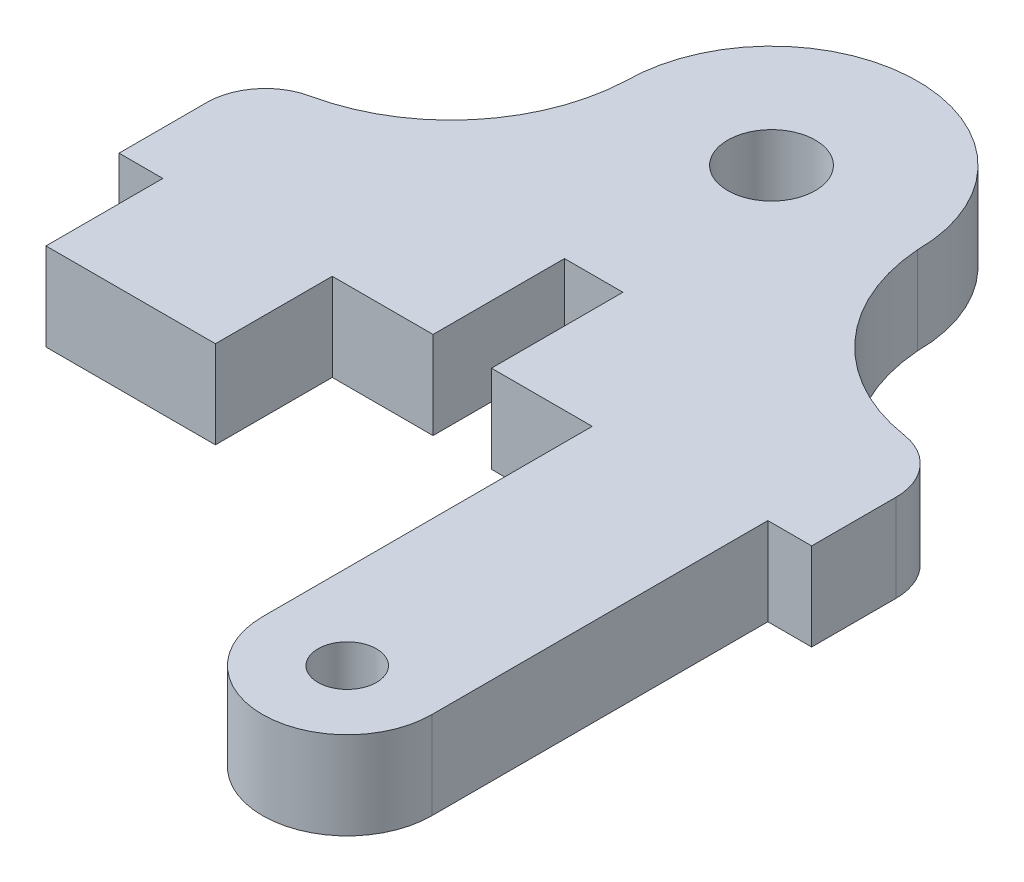
SolidWorks part; units mm, degrees
ref_plane "Front Plane" through (0, 0, 0) normal (0, 0, 1) x (1, 0, 0)
ref_plane "Top Plane" through (0, 0, 0) normal (0, 1, 0) x (1, 0, 0)
ref_plane "Right Plane" through (0, 0, 0) normal (1, 0, 0) x (0, 0, -1)
sketch "Sketch2" plane through (0, 0, 0) normal (0, 1, 0) x (1, 0, 0)
  line L0 (4.6686, -14.5944) -> (4.6686, -22.0944)
  line L1 (-11.5314, -10.8064) -> (-10.0314, -10.8064)
  line L2 (-10.0314, -10.8064) -> (-10.0314, -14.8064)
  line L3 (-10.0314, -14.8064) -> (-4.2314, -14.8064)
  line L5 (-11.5314, -10.8064) -> (-11.5314, -5.9738)
  line L7 (11.9686, -5.7619) -> (11.9686, -10.5944)
  line L8 (-4.2314, -14.8064) -> (-4.2314, -10.8064)
  line L9 (11.9686, -10.5944) -> (10.4686, -10.5944)
  line L10 (10.4686, -10.5944) -> (10.4686, -14.5944)
  line L12 (4.6686, -14.5944) -> (4.6686, -10.8064)
  line L13 (-4.2314, -10.8064) -> (-0.7814, -10.8064)
  line L16 (-0.7814, -10.8064) -> (-0.7814, -6.3064)
  line L17 (-0.7814, -6.3064) -> (1.2186, -6.3064)
  line L18 (1.2186, -6.3064) -> (1.2186, -10.8064)
  line L19 (1.2186, -10.8064) -> (4.6686, -10.8064)
  line L20 (10.4686, -22.0944) -> (10.4686, -14.5944)
  arc A0 (5, 0) -> (-5, 0) centre (0, 0) ccw
  arc A2 (-11.5314, -5.9738) -> (-5, 0) centre (-11.2526, 0.2788) ccw
  arc A3 (5, 0) -> (11.9686, -5.7619) centre (11.2434, 0.456) ccw
  arc A4 (4.6686, -22.0944) -> (10.4686, -22.0944) centre (7.5686, -22.0944) ccw
  point P10 (0, 0)
  dimension "D1" = 10
  dimension "D4" = 11.5
  dimension "D11" = 23.5
  dimension "D12" = 5.8
  dimension "D2" = 4
  dimension "D3" = 1.5
  dimension "D5" = 5.8
  dimension "D6" = 1.5
  dimension "D7" = 4
  dimension "D8" = 5.8
  dimension "D9" = 2
  dimension "D10" = 4.5
extrude "Boss-Extrude1" add sketch "Sketch2" along normal blind 3
sketch "Sketch3" plane through (0, 3, 0) normal (0, 1, 0) x (1, 0, 0)
  circle A0 centre (0, 0) radius 1.5
  dimension "D1" = 3
extrude "Cut-Extrude1" cut sketch "Sketch3" against normal blind 3
fillet "Fillet1" radius 2 2 edges at (-11.5314, 1.5, 5.9738) (11.9686, 1.5, 5.7619)
sketch "Sketch4" plane through (0, 3, 0) normal (0, 1, 0) x (1, 0, 0)
  circle A0 centre (7.5686, -22.0944) radius 1
extrude "Cut-Extrude2" cut sketch "Sketch4" against normal blind 10
